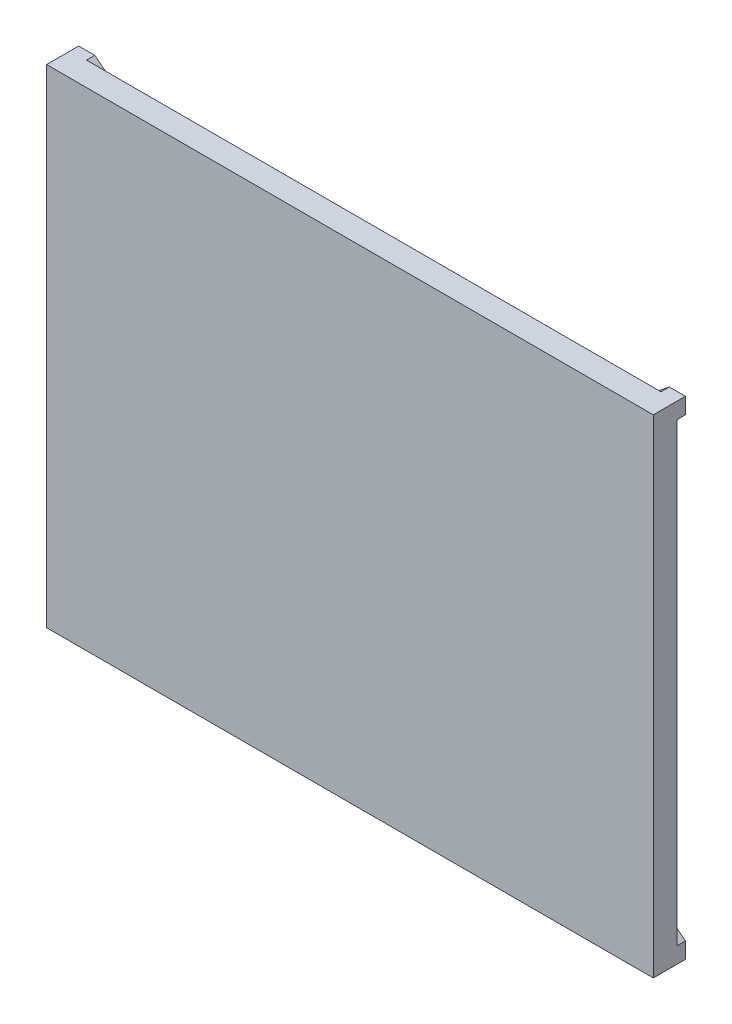
SolidWorks part; units mm, degrees
ref_plane "Front Plane" through (0, 0, 0) normal (0, 0, 1) x (1, 0, 0)
ref_plane "Top Plane" through (0, 0, 0) normal (0, 1, 0) x (1, 0, 0)
ref_plane "Right Plane" through (0, 0, 0) normal (1, 0, 0) x (0, 0, -1)
sketch "Sketch1" plane through (0, 0, 0) normal (0, 0, 1) x (1, 0, 0)
  line L1 (-510, -410) -> (510, -410)
  line L2 (-510, -410) -> (-510, 410)
  line L3 (-510, 410) -> (510, 410)
  line L4 (510, -410) -> (510, 410)
  line L5 (-510, -410) -> (510, 410) construction
  line L6 (-510, 410) -> (510, -410) construction
  point P0 (0, 0)
  dimension "D1" = 1020
  dimension "D2" = 820
extrude "Boss-Extrude1" add sketch "Sketch1" along normal blind 40
sketch "Sketch2" plane through (0, 0, 0) normal (0, 0, -1) x (-1, 0, 0)
  line L0 (-482.962, 410) -> (510, -382.962)
  line L1 (-510, 410) -> (510, 410) construction
  line L2 (510, 410) -> (510, -410) construction
  line L3 (510, -382.962) -> (510, -410)
  line L4 (510, -410) -> (-510, -410) construction
  line L5 (510, -410) -> (482.962, -410)
  line L6 (482.962, -410) -> (-510, 382.962)
  line L7 (-510, -410) -> (-510, 410) construction
  line L8 (-510, 382.962) -> (-510, 410)
  line L9 (-510, 410) -> (-482.962, 410)
  dimension "D1" = 38
  dimension "D2" = 19
extrude "Boss-Extrude2" add sketch "Sketch2" along normal blind 14
mirror "Mirror1" about plane through (0, 0, 0) normal (0, 1, 0) of "Boss-Extrude2"
